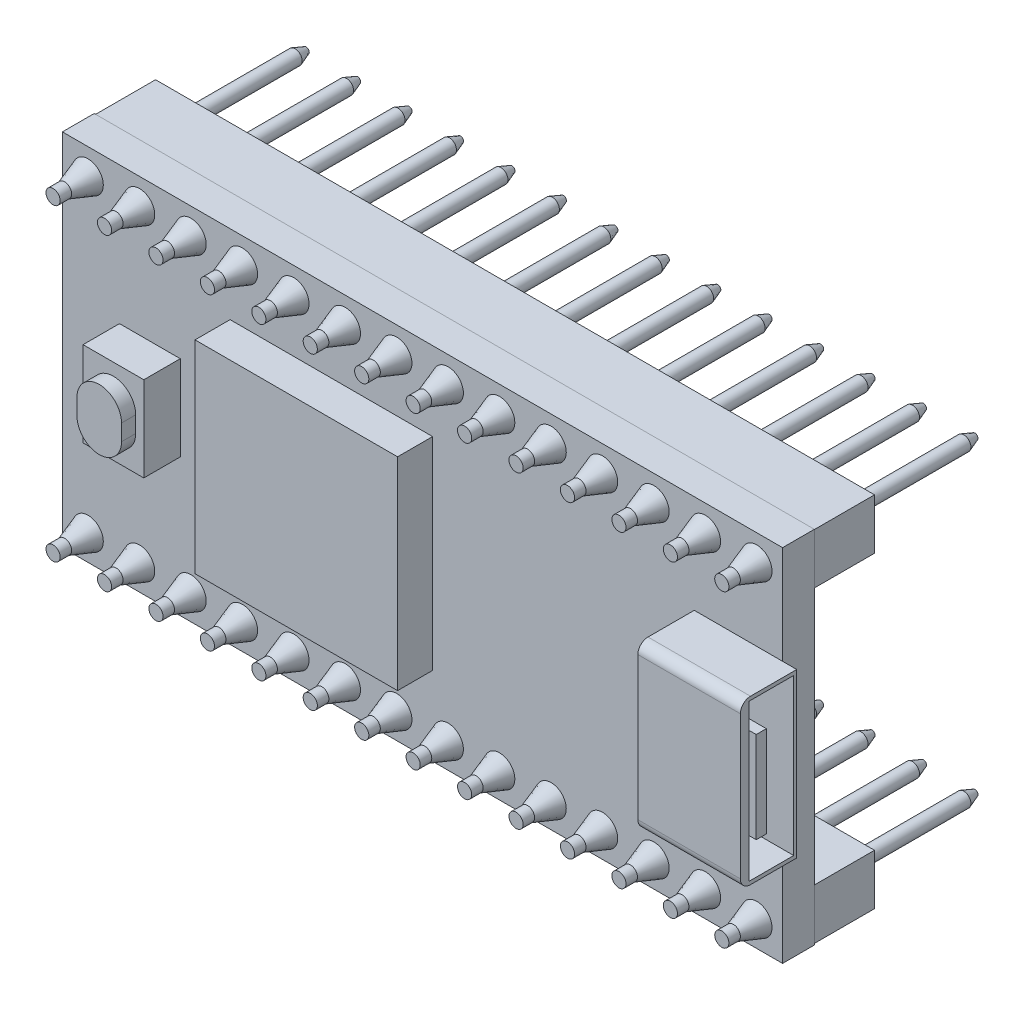
SolidWorks part; units mm, degrees
ref_plane "Vorne" through (0, 0, 0) normal (0, 0, 1) x (1, 0, 0)
ref_plane "Oben" through (0, 0, 0) normal (0, 1, 0) x (1, 0, 0)
ref_plane "Rechts" through (0, 0, 0) normal (1, 0, 0) x (0, 0, -1)
sketch "Skizze1" plane through (0, 0, 0) normal (0, 0, 1) x (1, 0, 0)
  line L0 (0, 44.7446) -> (0, 0) construction
  line L1 (-17.78, 8.89) -> (17.78, 8.89)
  line L2 (-17.78, 8.89) -> (-17.78, -8.89)
  line L3 (-17.78, -8.89) -> (17.78, -8.89)
  line L4 (17.78, 8.89) -> (17.78, -8.89)
  line L5 (0, 0) -> (42.4715, 0) construction
  dimension "D1" = 35.56
  dimension "D2" = 17.78
extrude "Aufsatz-Linear austragen1" add sketch "Skizze1" along normal blind 1.57
sketch "Skizze2" plane through (0, 0, 0) normal (0, 0, 1) x (1, 0, 0)
  line L0 (-16.51, -7.62) -> (16.51, -7.62) construction
  line L1 (16.51, -7.62) -> (16.51, 7.62) construction
  line L2 (16.51, 7.62) -> (-16.51, 7.62) construction
  line L3 (-16.51, 7.62) -> (-16.51, -7.62) construction
  line L4 (0, 11.9625) -> (0, 0) construction
  line L5 (0, 0) -> (13.3836, 0) construction
  circle A0 centre (-16.51, 7.62) radius 0.35
  circle A1 centre (-13.97, 7.62) radius 0.35
  circle A2 centre (-11.43, 7.62) radius 0.35
  circle A3 centre (-8.89, 7.62) radius 0.35
  circle A4 centre (-6.35, 7.62) radius 0.35
  circle A5 centre (-3.81, 7.62) radius 0.35
  circle A6 centre (-1.27, 7.62) radius 0.35
  circle A7 centre (1.27, 7.62) radius 0.35
  circle A8 centre (3.81, 7.62) radius 0.35
  circle A9 centre (6.35, 7.62) radius 0.35
  circle A10 centre (8.89, 7.62) radius 0.35
  circle A11 centre (11.43, 7.62) radius 0.35
  circle A12 centre (13.97, 7.62) radius 0.35
  circle A13 centre (16.51, 7.62) radius 0.35
  circle A14 centre (-16.51, 5.08) radius 0.35 construction
  circle A15 centre (-16.51, 2.54) radius 0.35 construction
  circle A16 centre (-16.51, 0) radius 0.35 construction
  circle A17 centre (-16.51, -2.54) radius 0.35 construction
  circle A18 centre (-16.51, -5.08) radius 0.35 construction
  circle A19 centre (-16.51, -7.62) radius 0.35
  circle A20 centre (-13.97, -7.62) radius 0.35
  circle A21 centre (-11.43, -7.62) radius 0.35
  circle A22 centre (-8.89, -7.62) radius 0.35
  circle A23 centre (-6.35, -7.62) radius 0.35
  circle A24 centre (-3.81, -7.62) radius 0.35
  circle A25 centre (-1.27, -7.62) radius 0.35
  circle A26 centre (1.27, -7.62) radius 0.35
  circle A27 centre (3.81, -7.62) radius 0.35
  circle A28 centre (6.35, -7.62) radius 0.35
  circle A29 centre (8.89, -7.62) radius 0.35
  circle A30 centre (11.43, -7.62) radius 0.35
  circle A31 centre (13.97, -7.62) radius 0.35
  circle A32 centre (16.51, -7.62) radius 0.35
  dimension "D2" = 0.7
  dimension "D4" = 2.54
  dimension "D6" = 7.62
  dimension "D1" = 16.51
  dimension "D3" = 14
  dimension "D5" = 7
  dimension "D7" = 14
extrude "Aufsatz-Linear austragen2" add sketch "Skizze2" along normal blind 3.3 and the other way blind 9.2
sketch "Skizze3" plane through (0, 0, 1.57) normal (0, 0, 1) x (1, 0, 0)
  line L0 (4.4102, 0) -> (0, 0) construction
  line L1 (0, 0) -> (0, 3.8724) construction
  line L2 (17.78, -8.89) -> (17.78, 8.89) construction
  line L3 (18.48, -4.03) -> (13.42, -4.03)
  line L4 (18.48, -4.03) -> (18.48, 4.03)
  line L5 (18.48, 4.03) -> (13.42, 4.03)
  line L6 (13.42, -4.03) -> (13.42, 4.03)
  dimension "D1" = 8.06
  dimension "D2" = 0.7
  dimension "D3" = 5.06
extrude "Aufsatz-Linear austragen3" add sketch "Skizze3" along normal blind 2.785
sketch "Skizze4" plane through (0, 0, 1.57) normal (0, 0, 1) x (1, 0, 0)
  line L0 (-13.46, 0) -> (0, 0) construction
  line L1 (-11.96, -2.1) -> (-14.96, -2.1)
  line L2 (-11.96, -2.1) -> (-11.96, 2.1)
  line L3 (-11.96, 2.1) -> (-14.96, 2.1)
  line L4 (-14.96, -2.1) -> (-14.96, 2.1)
  line L5 (0, 0) -> (0, 4.5772) construction
  line L6 (-13.46, 0) -> (-13.46, 4.5772) construction
  dimension "D1" = 13.46
  dimension "D2" = 4.2
  dimension "D3" = 3
extrude "Aufsatz-Linear austragen4" add sketch "Skizze4" along normal blind 1.8
sketch "Skizze5" plane through (0, 0, 3.37) normal (0, 0, 1) x (1, 0, 0)
  line L0 (-13.46, 0) -> (0, 0) construction
  line L1 (0, 0) -> (0, 4.3496) construction
  line L2 (-13.46, 0) -> (-13.46, 4.3496) construction
  line L3 (-13.46, -0.4) -> (-13.46, 0.4) construction
  line L4 (-14.56, -0.4) -> (-14.56, 0.4)
  line L5 (-12.36, -0.4) -> (-12.36, 0.4)
  arc A0 (-14.56, -0.4) -> (-12.36, -0.4) centre (-13.46, -0.4) ccw
  arc A1 (-12.36, 0.4) -> (-14.56, 0.4) centre (-13.46, 0.4) ccw
  point P7 (-13.46, 0)
  dimension "D3" = 3
  dimension "D1" = 13.46
  dimension "D2" = 2.2
extrude "Aufsatz-Linear austragen5" add sketch "Skizze5" along normal blind 0.7
sketch "Skizze6" plane through (0, 0, 1.57) normal (0, 0, 1) x (1, 0, 0)
  line L0 (0, 3.0998) -> (0, 0) construction
  line L1 (0.5, -5) -> (-9.5, -5)
  line L2 (0.5, -5) -> (0.5, 5)
  line L3 (0.5, 5) -> (-9.5, 5)
  line L4 (-9.5, -5) -> (-9.5, 5)
  line L5 (0, 0) -> (-4.5, 0) construction
  line L6 (-4.5, 0) -> (-4.5, 2.7885) construction
  dimension "D1" = 10
  dimension "D2" = 4.5
extrude "Aufsatz-Linear austragen6" add sketch "Skizze6" along normal blind 1.73
sketch "Skizze7" plane through (18.48, 0, 0) normal (1, 0, 0) x (0, 0, -1)
  line L0 (0, 0) -> (-2.82, 0) construction
  line L1 (-3.92, 3.85) -> (-1.72, 3.85)
  line L2 (-3.92, 3.85) -> (-3.92, -3.85)
  line L3 (-3.92, -3.85) -> (-1.72, -3.85)
  line L4 (-1.72, 3.85) -> (-1.72, -3.85)
  line L6 (0, -10.2353) -> (0, 0) construction
  line L7 (-2.82, 0) -> (-2.82, -2.3127) construction
  line L9 (-3.57, -2.25) -> (-3.07, -2.25)
  line L10 (-3.57, -2.25) -> (-3.57, 2.25)
  line L11 (-3.57, 2.25) -> (-3.07, 2.25)
  line L12 (-3.07, -2.25) -> (-3.07, 2.25)
  dimension "D1" = 2.82
  dimension "D2" = 2.2
  dimension "D3" = 7.7
  dimension "D4" = 0.25
  dimension "D5" = 0.5
  dimension "D6" = 4.5
extrude "Schnitt-Linear austragen1" cut sketch "Skizze7" against normal blind 4.5
fillet "Verrundung1" radius 0.5 2 edges at (15.95, -4.03, 4.355) (15.95, 4.03, 4.355)
sketch "Skizze8" plane through (0, 0, 0) normal (0, 0, 1) x (1, 0, 0)
  line L0 (-17.75, -8.85) -> (17.75, -8.85)
  line L1 (-17.75, 8.85) -> (17.75, 8.85)
  line L2 (-17.75, 8.85) -> (-17.75, -8.85) construction
  line L5 (0, 10.8356) -> (0, 0) construction
  line L6 (0, 0) -> (20.8369, 0) construction
  line L8 (17.75, 8.85) -> (17.75, 6.35)
  line L9 (17.75, 6.35) -> (-15.21, 6.35)
  line L10 (-15.21, 6.35) -> (-15.21, -6.35) construction
  line L11 (-15.21, -6.35) -> (17.75, -6.35)
  line L12 (17.75, -6.35) -> (17.75, -8.85)
  line L13 (-15.21, -6.35) -> (-17.75, -6.35)
  line L14 (-17.75, -6.35) -> (-17.75, -8.85)
  line L15 (-15.21, 6.35) -> (-17.75, 6.35)
  line L16 (-17.75, 6.35) -> (-17.75, 8.85)
  dimension "D1" = 35.5
  dimension "D2" = 17.7
  dimension "D3" = 12.7
  dimension "D4" = 2.54
extrude "Aufsatz-Linear austragen8" add sketch "Skizze8" against normal blind 3
sketch "Skizze9" plane through (0, 0, 1.57) normal (0, 0, 1) x (1, 0, 0)
  line L0 (-16.51, -7.62) -> (16.51, -7.62) construction
  line L1 (16.51, -7.62) -> (16.51, 7.62) construction
  line L2 (16.51, 7.62) -> (-16.51, 7.62) construction
  line L3 (-16.51, 7.62) -> (-16.51, -7.62) construction
  line L4 (0, 12.1916) -> (0, 0) construction
  line L5 (0, 0) -> (23.4263, 0) construction
  circle A0 centre (-16.51, 7.62) radius 0.75
  circle A33 centre (-13.97, 7.62) radius 0.75
  circle A34 centre (-11.43, 7.62) radius 0.75
  circle A35 centre (-8.89, 7.62) radius 0.75
  circle A36 centre (-6.35, 7.62) radius 0.75
  circle A37 centre (-3.81, 7.62) radius 0.75
  circle A38 centre (-1.27, 7.62) radius 0.75
  circle A39 centre (1.27, 7.62) radius 0.75
  circle A40 centre (3.81, 7.62) radius 0.75
  circle A41 centre (6.35, 7.62) radius 0.75
  circle A42 centre (8.89, 7.62) radius 0.75
  circle A43 centre (11.43, 7.62) radius 0.75
  circle A44 centre (13.97, 7.62) radius 0.75
  circle A45 centre (16.51, 7.62) radius 0.75
  circle A46 centre (-16.51, 5.08) radius 0.75 construction
  circle A47 centre (-16.51, 2.54) radius 0.75 construction
  circle A48 centre (-16.51, 0) radius 0.75 construction
  circle A49 centre (-16.51, -2.54) radius 0.75 construction
  circle A50 centre (-16.51, -5.08) radius 0.75 construction
  circle A51 centre (-16.51, -7.62) radius 0.75
  circle A52 centre (-13.97, -7.62) radius 0.75
  circle A53 centre (-11.43, -7.62) radius 0.75
  circle A54 centre (-8.89, -7.62) radius 0.75
  circle A55 centre (-6.35, -7.62) radius 0.75
  circle A56 centre (-3.81, -7.62) radius 0.75
  circle A57 centre (-1.27, -7.62) radius 0.75
  circle A58 centre (1.27, -7.62) radius 0.75
  circle A59 centre (3.81, -7.62) radius 0.75
  circle A60 centre (6.35, -7.62) radius 0.75
  circle A61 centre (8.89, -7.62) radius 0.75
  circle A62 centre (11.43, -7.62) radius 0.75
  circle A63 centre (13.97, -7.62) radius 0.75
  circle A64 centre (16.51, -7.62) radius 0.75
  dimension "D3" = 1.5
  dimension "D5" = 2.54
  dimension "D7" = 14
  dimension "D1" = 33.02
  dimension "D2" = 15.24
  dimension "D4" = 14
  dimension "D6" = 7
extrude "Aufsatz-Linear austragen9" add sketch "Skizze9" along normal blind 1.7 draft 19
chamfer "Fase1" distance 0.2 angle 70 28 edges at (16.86, -7.62, -9.2) (14.32, -7.62, -9.2) (11.78, -7.62, -9.2) (9.24, -7.62, -9.2) (6.7, -7.62, -9.2) (4.16, -7.62, -9.2) (1.62, -7.62, -9.2) (-0.92, -7.62, -9.2) (-3.46, -7.62, -9.2) (-6, -7.62, -9.2) (-8.54, -7.62, -9.2) (-11.08, -7.62, -9.2) (-13.62, -7.62, -9.2) (-16.16, -7.62, -9.2) (16.86, 7.62, -9.2) (14.32, 7.62, -9.2) (11.78, 7.62, -9.2) (9.24, 7.62, -9.2) (6.7, 7.62, -9.2) (4.16, 7.62, -9.2) (1.62, 7.62, -9.2) (-0.92, 7.62, -9.2) (-3.46, 7.62, -9.2) (-6, 7.62, -9.2) (-8.54, 7.62, -9.2) (-11.08, 7.62, -9.2) (-13.62, 7.62, -9.2) (-16.16, 7.62, -9.2)
